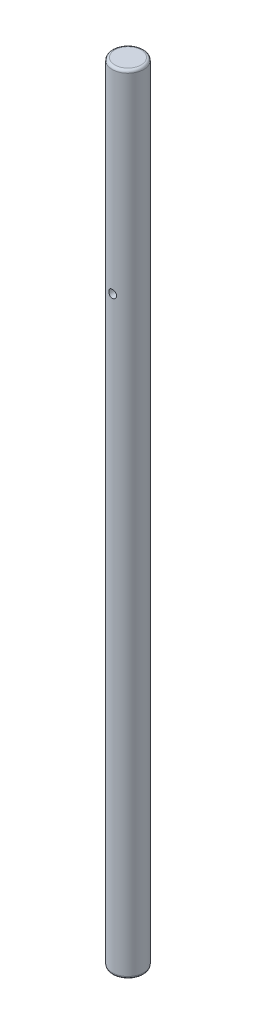
SolidWorks part; units mm, degrees
ref_plane "Front Plane" through (0, 0, 0) normal (0, 0, 1) x (1, 0, 0)
ref_plane "Top Plane" through (0, 0, 0) normal (0, 1, 0) x (1, 0, 0)
ref_plane "Right Plane" through (0, 0, 0) normal (1, 0, 0) x (0, 0, -1)
sketch "Sketch1" plane through (0, 0, 0) normal (0, 1, 0) x (1, 0, 0)
  circle A0 centre (0, 0) radius 6
  dimension "D1" = 12
extrude "Boss-Extrude1" add sketch "Sketch1" along normal blind 300
sketch "Sketch2" plane through (0, 0, 0) normal (0, -1, 0) x (1, 0, 0)
  circle A0 centre (0, 0) radius 2.5
  dimension "D1" = 5
extrude "Cut-Extrude1" cut sketch "Sketch2" against normal blind 20
sketch "Sketch3" plane through (0, 0, 0) normal (0, 0, 1) x (1, 0, 0)
  line L0 (-6, 0) -> (6, 0) construction
  circle A0 centre (0, 5) radius 1.5
  dimension "D1" = 3
  dimension "D2" = 5
extrude "Cut-Extrude2" cut sketch "Sketch3" against normal blind 20
fillet "Fillet1" radius 1 2 edges at (0, 0, 6) (0, 300, 6)
sketch "Sketch4" plane through (0, 0, 0) normal (0, 0, 1) x (1, 0, 0)
  line L0 (5, 300) -> (-5, 300) construction
  circle A0 centre (0, 225) radius 1.5
  dimension "D1" = 75
  dimension "D2" = 3
extrude "Cut-Extrude3" cut sketch "Sketch4" against normal through all both and the other way through all
